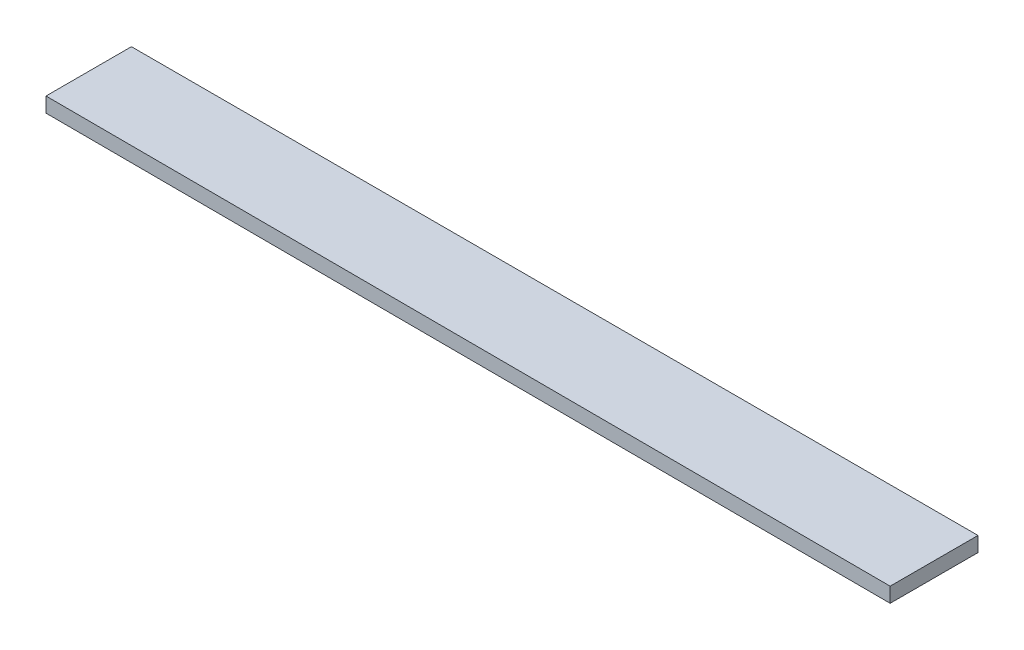
SolidWorks part; units mm, degrees
ref_plane "Plan de face" through (0, 0, 0) normal (0, 0, 1) x (1, 0, 0)
ref_plane "Plan de dessus" through (0, 0, 0) normal (0, 1, 0) x (1, 0, 0)
ref_plane "Plan de droite" through (0, 0, 0) normal (1, 0, 0) x (0, 0, -1)
sketch "Esquisse1" plane through (0, 0, 0) normal (0, 1, 0) x (1, 0, 0)
  line L0 (113.8362, -0.3259) -> (113.8362, 11.4881)
  line L1 (113.8362, 11.4881) -> (0, 11.4881)
  line L2 (0, 11.4881) -> (0, 0)
  line L3 (0, 0) -> (113.8362, -0.3259)
  point P4 (0, 0)
extrude "Boss.-Extru.1" add sketch "Esquisse1" along normal blind 2
